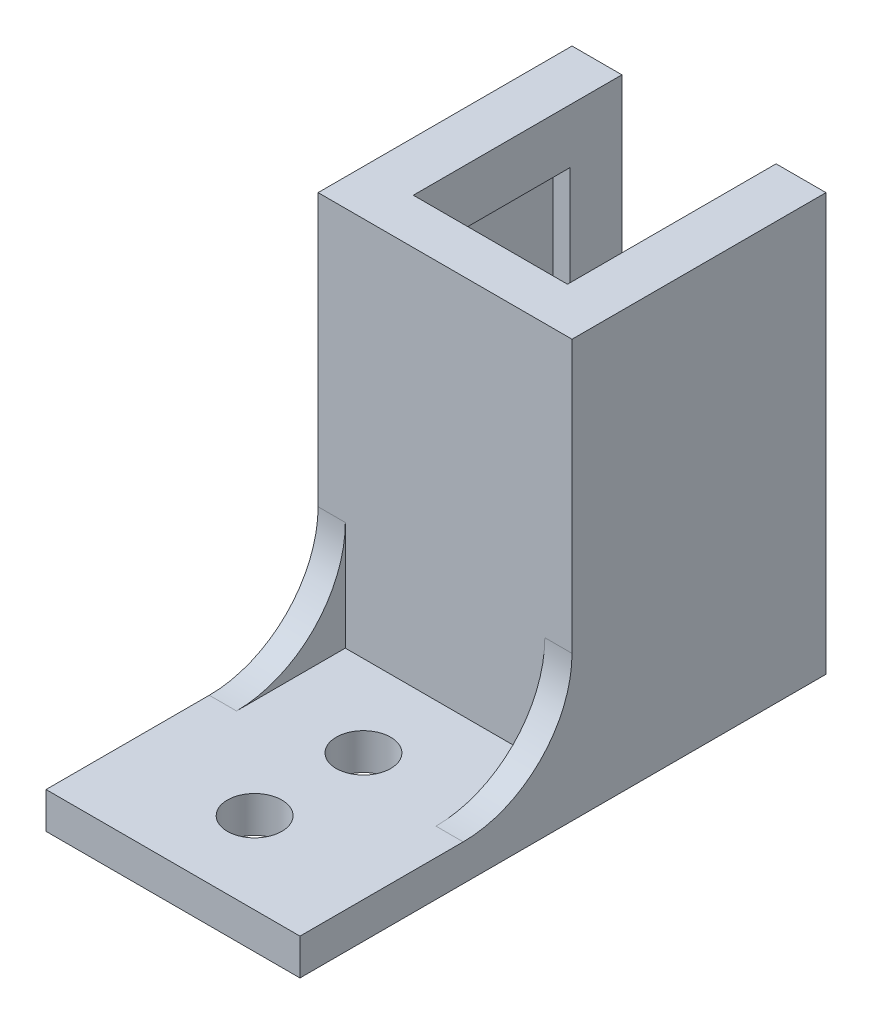
SolidWorks part; units mm, degrees
ref_plane "Front Plane" through (0, 0, 0) normal (0, 0, 1) x (1, 0, 0)
ref_plane "Top Plane" through (0, 0, 0) normal (0, 1, 0) x (1, 0, 0)
ref_plane "Right Plane" through (0, 0, 0) normal (1, 0, 0) x (0, 0, -1)
sketch "Sketch1" plane through (0, 0, 0) normal (0, 0, 1) x (1, 0, 0)
  line L1 (7, 11.5) -> (-7, 11.5)
  line L2 (7, 11.5) -> (7, -11.5)
  line L3 (7, -11.5) -> (-7, -11.5)
  line L4 (-7, 11.5) -> (-7, -11.5)
  line L5 (7, 11.5) -> (-7, -11.5) construction
  line L6 (7, -11.5) -> (-7, 11.5) construction
  point P0 (0, 0)
  dimension "D1" = 14
  dimension "D2" = 23
extrude "Boss-Extrude1" add sketch "Sketch1" along normal blind 14
sketch "Sketch2" plane through (0, -11.5, 0) normal (0, -1, 0) x (1, 0, 0)
  line L1 (5.2, 2.85) -> (-5.2, 2.85)
  line L2 (5.2, 2.85) -> (5.2, 11.5)
  line L3 (5.2, 11.5) -> (-5.2, 11.5)
  line L4 (-5.2, 2.85) -> (-5.2, 11.5)
  line L8 (4.25, 2.85) -> (-4.25, 2.85)
  line L9 (4.25, 2.85) -> (4.25, 0)
  line L10 (4.25, 0) -> (-4.25, 0)
  line L11 (-4.25, 2.85) -> (-4.25, 0)
  point P4 (0, 2.85)
  point P16 (0, 0)
  dimension "D1" = 11.5
  dimension "D2" = 8.65
  dimension "D3" = 10.4
  dimension "D4" = 8.5
extrude "Cut-Extrude1" cut sketch "Sketch2" against normal blind 20
sketch "Sketch3" plane through (0, -11.5, 0) normal (0, -1, 0) x (1, 0, 0)
  line L0 (0, 18.5) -> (0, 24.5) construction
  line L1 (7, 14) -> (-7, 14)
  line L2 (7, 14) -> (7, 29)
  line L3 (7, 29) -> (-7, 29)
  line L4 (-7, 14) -> (-7, 29)
  circle A0 centre (0, 18.5) radius 1.5
  circle A1 centre (0, 24.5) radius 1.5
  point P10 (0, 21.5)
  point P11 (-7, 21.5)
  point P12 (7, 27.6431)
  point P13 (-0.1536, 24.1622)
  point P14 (0, 0)
  point P15 (0, 14)
  dimension "D1" = 3
  dimension "D2" = 6
  dimension "D3" = 4.5
extrude "Boss-Extrude2" add sketch "Sketch3" against normal blind 2
sketch "Sketch4" plane through (-7, 0, 0) normal (-1, 0, 0) x (0, 0, 1)
  line L1 (29, -9.5) -> (14, -9.5) construction
  line L2 (14, 11.5) -> (14, -9.5) construction
  line L3 (14, -3.5) -> (14, -9.5)
  line L4 (14, -9.5) -> (20, -9.5)
  arc A0 (20, -9.5) -> (14, -3.5) centre (20, -3.5) cw
  dimension "D1" = 6
extrude "Boss-Extrude3" add sketch "Sketch4" against normal blind 1.5
mirror "Mirror1" about plane through (0, 0, 0) normal (1, 0, 0) of "Boss-Extrude3"
sketch "Sketch5" plane through (0, 8.5, 0) normal (0, -1, 0) x (1, 0, 0)
  line L0 (5.2, 11.5) -> (-5.2, 11.5) construction
  line L1 (4.25, 0) -> (-4.25, 0)
  line L2 (4.25, 0) -> (4.25, 11.5)
  line L3 (4.25, 11.5) -> (-4.25, 11.5)
  line L4 (-4.25, 0) -> (-4.25, 11.5)
  line L5 (7, 0) -> (4.25, 0) construction
  line L6 (-4.25, 0) -> (4.25, 0) construction
  point P7 (-4.25, 2)
  point P9 (-4.25, 0)
  point P11 (4.25, 0)
  point P16 (3.9378, 0)
extrude "Cut-Extrude2" cut sketch "Sketch5" against normal through all
sketch "Sketch6" plane through (0, 0, 0) normal (0, 0, -1) x (-1, 0, 0)
  line L0 (-7, 11.5) -> (-7, -11.5) construction
  line L1 (-7, 0) -> (7, 0)
  line L2 (-7, 0) -> (-7, -11.5)
  line L3 (-7, -11.5) -> (7, -11.5)
  line L4 (7, 0) -> (7, -11.5)
extrude "Cut-Extrude3" [suppressed] cut sketch "Sketch6" against normal through all
